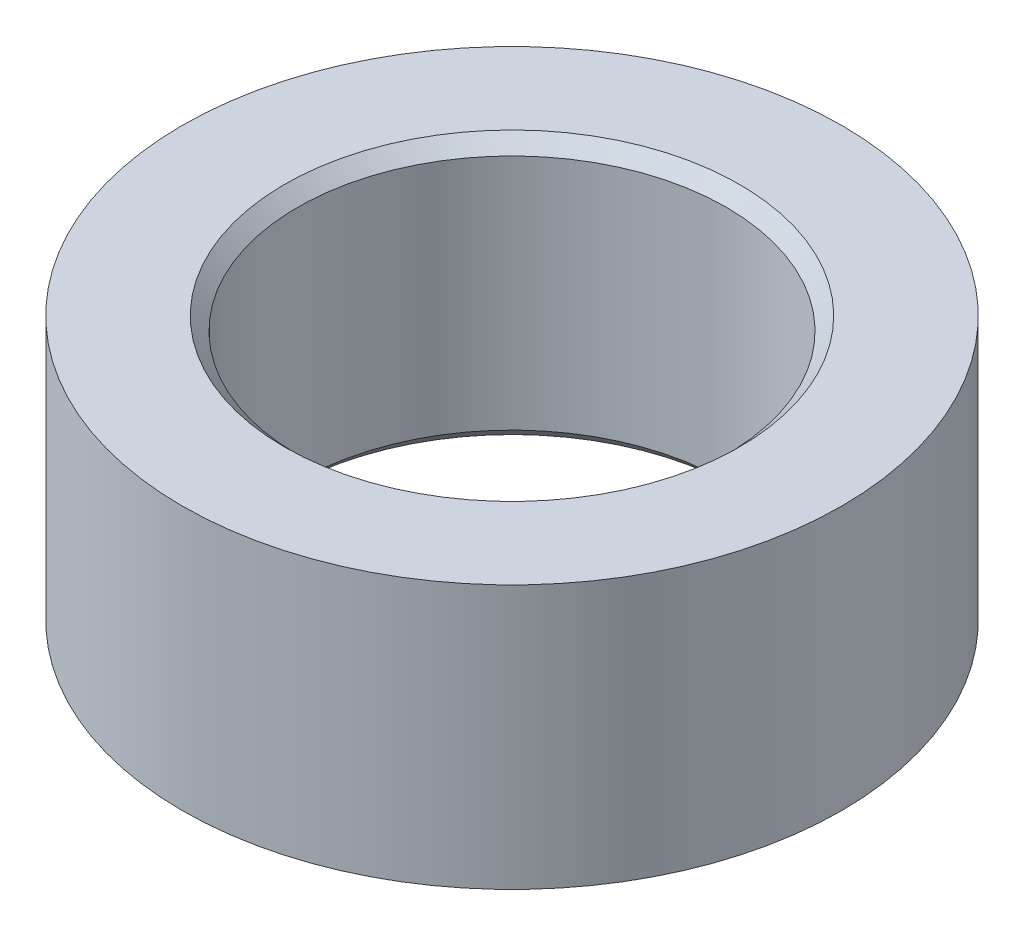
SolidWorks part; units mm, degrees
material "PLA/ABS"
ref_plane "Front Plane" through (0, 0, 0) normal (0, 0, 1) x (1, 0, 0)
ref_plane "Top Plane" through (0, 0, 0) normal (0, 1, 0) x (1, 0, 0)
ref_plane "Right Plane" through (0, 0, 0) normal (1, 0, 0) x (0, 0, -1)
other "Bounding Box"
ref_plane "Default Plane" through (-8.9266, -12.7485, 0) normal (-0.1736, 0.9848, 0) x (0.9848, 0.1736, 0)
sketch "Sketch1" plane through (0, 0, 0) normal (0, 1, 0) x (1, 0, 0)
  circle A0 centre (0, 0) radius 4.1275
  circle A1 centre (0, 0) radius 6.35
  dimension "D1" = 8.255
  dimension "D2" = 12.7
extrude "Boss-Extrude1" add sketch "Sketch1" along normal blind 5.08
chamfer "Chamfer1" distance 0.254 angle 45 2 edges at (0, 0, 4.1275) (0, 5.08, 4.1275)
